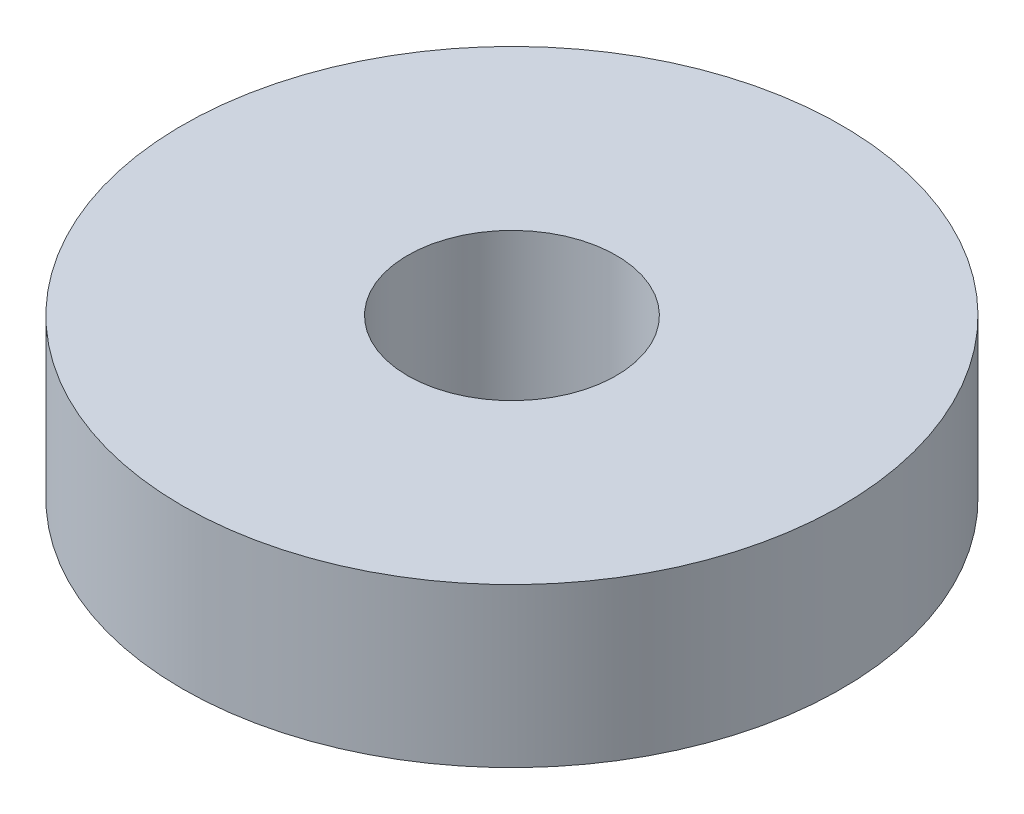
SolidWorks part; units mm, degrees
ref_plane "Front Plane" through (0, 0, 0) normal (0, 0, 1) x (1, 0, 0)
ref_plane "Top Plane" through (0, 0, 0) normal (0, 1, 0) x (1, 0, 0)
ref_plane "Right Plane" through (0, 0, 0) normal (1, 0, 0) x (0, 0, -1)
sketch "Sketch1" plane through (0, 0, 0) normal (0, 1, 0) x (1, 0, 0)
  circle A0 centre (0, 0) radius 3.95
  circle A1 centre (0, 0) radius 1.25
  dimension "D1" = 7.9
  dimension "D2" = 2.5
extrude "Boss-Extrude1" add sketch "Sketch1" along normal blind 1.9
